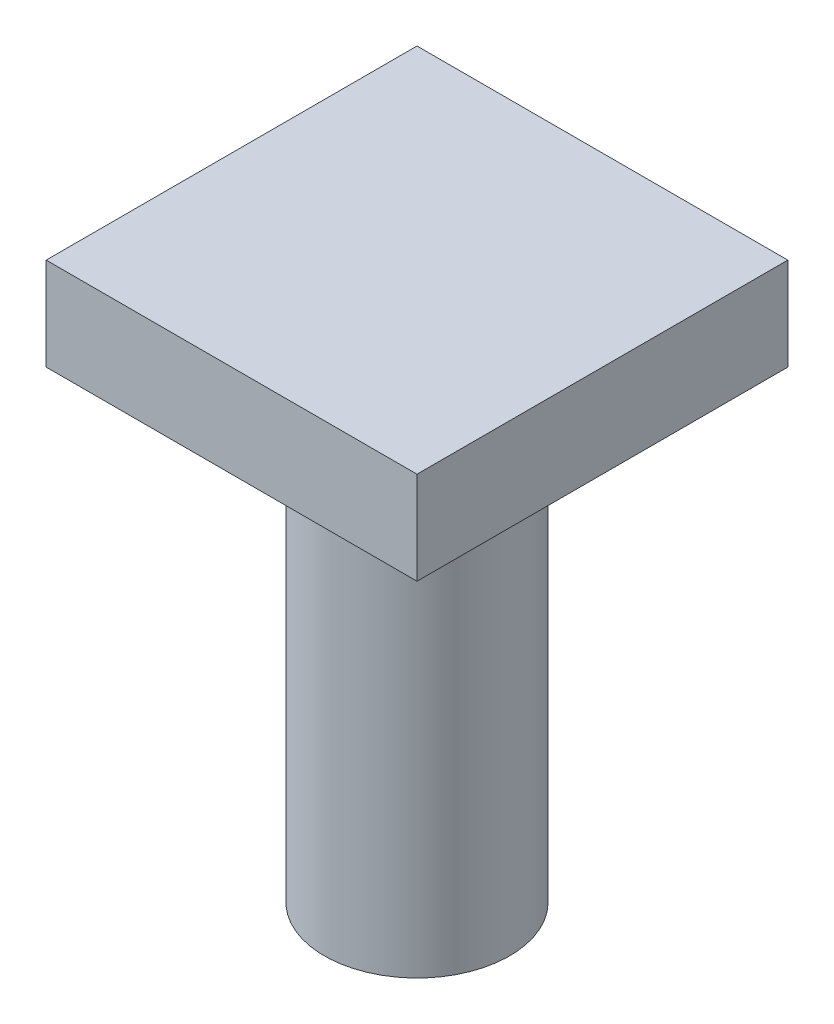
SolidWorks part; units mm, degrees
ref_plane "Спереди" through (0, 0, 0) normal (0, 0, 1) x (1, 0, 0)
ref_plane "Сверху" through (0, 0, 0) normal (0, 1, 0) x (1, 0, 0)
ref_plane "Справа" through (0, 0, 0) normal (1, 0, 0) x (0, 0, -1)
sketch "Эскиз1" plane through (0, 0, 0) normal (0, 1, 0) x (1, 0, 0)
  line L1 (-10, 10) -> (10, 10)
  line L2 (-10, 10) -> (-10, -10)
  line L3 (-10, -10) -> (10, -10)
  line L4 (10, 10) -> (10, -10)
  line L5 (-10, 10) -> (10, -10) construction
  line L6 (-10, -10) -> (10, 10) construction
  point P0 (0, 0)
extrude "Бобышка-Вытянуть1" add sketch "Эскиз1" along normal blind 30
sketch "Эскиз3" plane through (0, 0, 0) normal (0, -1, 0) x (1, 0, 0)
  line L0 (10, -10) -> (10, 10)
  line L1 (10, 10) -> (-10, 10)
  line L2 (-10, 10) -> (-10, -10)
  line L3 (-10, -10) -> (10, -10)
  circle A0 centre (0, 0) radius 5
extrude "Вырез-Вытянуть1" cut sketch "Эскиз3" against normal blind 25
